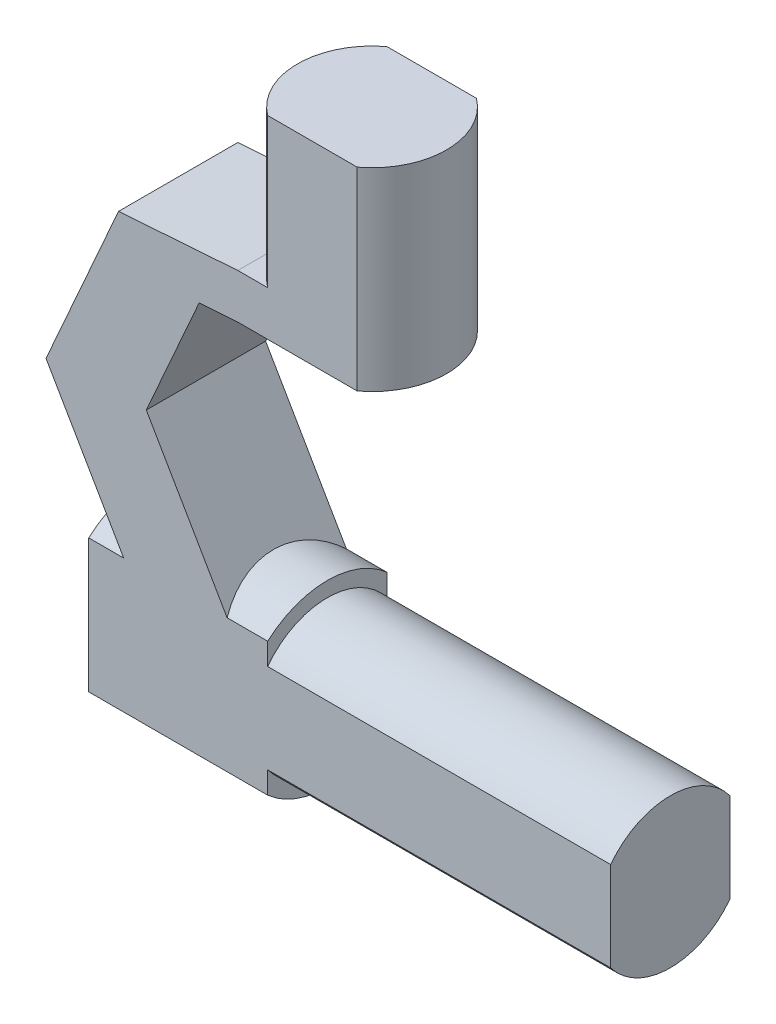
SolidWorks part; units mm, degrees
ref_plane "Alzado" through (0, 0, 0) normal (0, 0, 1) x (1, 0, 0)
ref_plane "Planta" through (0, 0, 0) normal (0, 1, 0) x (1, 0, 0)
ref_plane "Vista lateral" through (0, 0, 0) normal (1, 0, 0) x (0, 0, -1)
sketch "Croquis1" plane through (0, 0, 0) normal (0, 1, 0) x (1, 0, 0)
  circle A0 centre (0, 0) radius 5
  dimension "D1" = 10
extrude "Saliente-Extruir1" add sketch "Croquis1" along normal blind 3
sketch "Croquis2" plane through (0, 0, 0) normal (0, 0, 1) x (1, 0, 0)
  line L0 (-5, 3) -> (-13, 2.433)
  line L1 (-13, 2.433) -> (-17.8632, -8.5374)
  line L2 (-17.8632, -8.5374) -> (-8.3258, -25)
  line L3 (-8.3258, -25) -> (-1.3916, -25)
  line L4 (-1.3916, -25) -> (-11.1392, -8.1746)
  line L5 (-11.1392, -8.1746) -> (-7.597, -0.1841)
  line L6 (-7.597, -0.1841) -> (-5, 0)
  line L8 (-5, 0) -> (0, 0)
  line L9 (0, 0) -> (0, 3)
  line L10 (5, 3) -> (-5, 3) construction
  line L11 (0, 3) -> (-5, 3)
  dimension "D1" = 6
  dimension "D2" = 8
  dimension "D3" = 25
  dimension "D4" = 6
  dimension "D5" = 12
extrude "Saliente-Extruir2" add sketch "Croquis2" along normal mid plane 8
sketch "Croquis3" plane through (0, 3, 0) normal (0, 1, 0) x (1, 0, 0)
  circle A0 centre (0, 0) radius 5
  dimension "D1" = 10
sketch "Croquis4" plane through (0, 0, 0) normal (1, 0, 0) x (0, 0, -1)
  line L0 (0, -25) -> (0, -22) construction
  line L1 (-4, -25) -> (4, -25) construction
  circle A0 centre (0, -22) radius 5
  dimension "D1" = 10
  dimension "D2" = 3
extrude "Saliente-Extruir3" add sketch "Croquis4" against normal blind 15
sketch "Croquis6" plane through (0, 0, 0) normal (1, 0, 0) x (0, 0, -1)
  circle A0 centre (0, -22) radius 5
  dimension "D1" = 10
extrude "Saliente-Extruir5" add sketch "Croquis6" along normal blind 20
extrude "Saliente-Extruir7" add sketch "Croquis3" along normal blind 10
sketch "Croquis12" plane through (-15, 0, 0) normal (-1, 0, 0) x (0, 0, 1)
  circle A0 centre (0, -22) radius 6
  dimension "D1" = 12
extrude "Saliente-Extruir8" add sketch "Croquis12" against normal blind 12
sketch "Croquis11" plane through (0, 13, 0) normal (0, 1, 0) x (1, 0, 0)
  line L0 (-33, 4) -> (27, 4)
  line L1 (27, 4) -> (27, 9)
  line L2 (27, 9) -> (-33, 9)
  line L3 (-33, 9) -> (-33, 4)
  line L8 (0, 0) -> (3.8773, 0) construction
  line L9 (27, -9) -> (-33, -9)
  line L10 (27, -4) -> (27, -9)
  line L11 (-33, -4) -> (27, -4)
  line L12 (-33, -9) -> (-33, -4)
  point P8 (-3, 4)
  dimension "D1" = 60
  dimension "D2" = 5
extrude "Cortar-Extruir4" cut sketch "Croquis11" against normal through all
